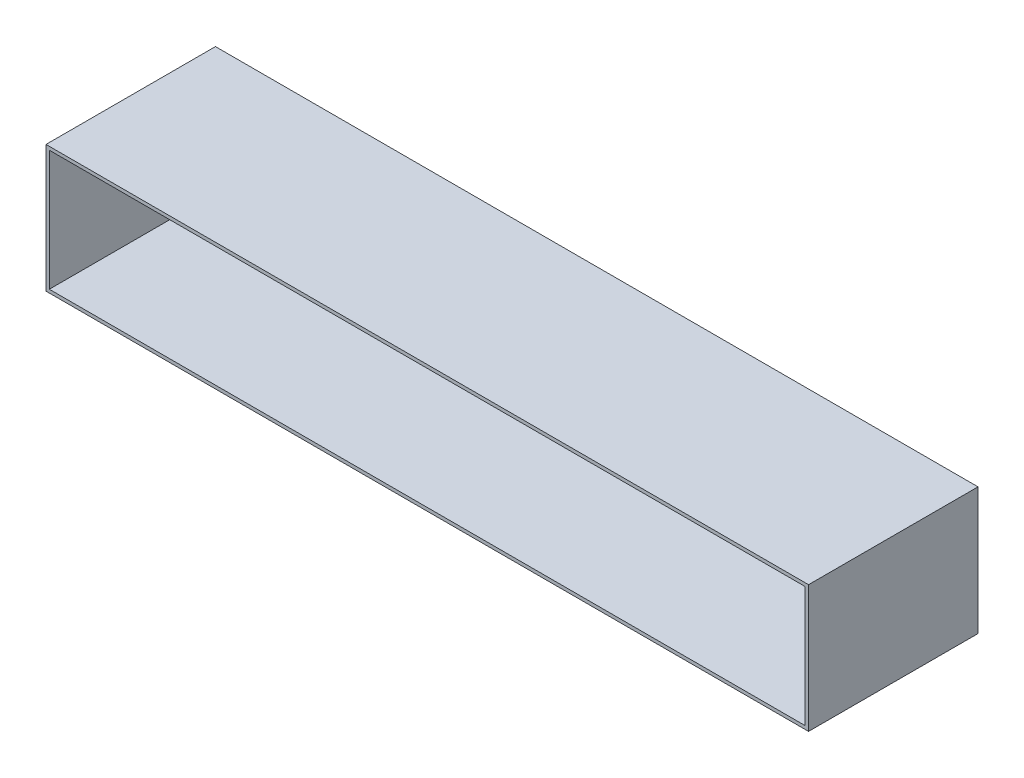
SolidWorks part; units mm, degrees
ref_plane "Спереди" through (0, 0, 0) normal (0, 0, 1) x (1, 0, 0)
ref_plane "Сверху" through (0, 0, 0) normal (0, 1, 0) x (1, 0, 0)
ref_plane "Справа" through (0, 0, 0) normal (1, 0, 0) x (0, 0, -1)
sketch "Эскиз1" plane through (0, 0, 0) normal (0, 0, 1) x (1, 0, 0)
  line L0 (-226.6, 36.1) -> (226.6, 36.1)
  line L1 (-228.6, 38.1) -> (228.6, 38.1)
  line L2 (-228.6, 38.1) -> (-228.6, -38.1)
  line L3 (-228.6, -38.1) -> (228.6, -38.1)
  line L4 (228.6, 38.1) -> (228.6, -38.1)
  line L5 (-228.6, 38.1) -> (228.6, -38.1) construction
  line L6 (-228.6, -38.1) -> (228.6, 38.1) construction
  line L7 (226.6, 36.1) -> (226.6, -36.1)
  line L8 (-226.6, -36.1) -> (226.6, -36.1)
  line L9 (-226.6, 36.1) -> (-226.6, -36.1)
  point P0 (0, 0)
  dimension "D1" = 457.2
  dimension "D2" = 76.2
  dimension "D3" = 2
extrude "Бобышка-Вытянуть1" add sketch "Эскиз1" along normal mid plane 101.6
